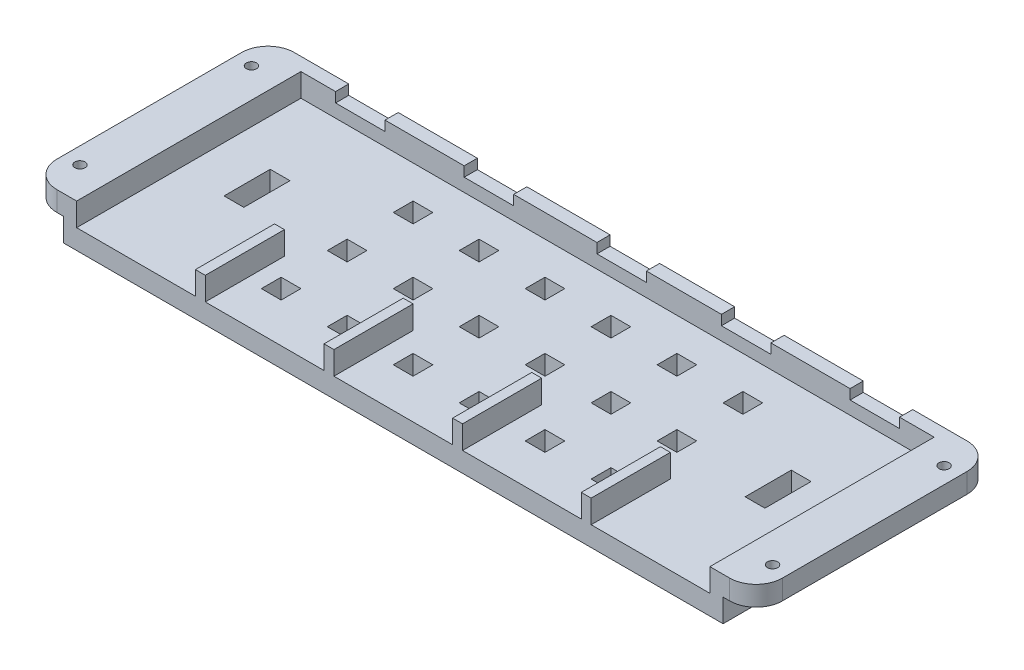
SolidWorks part; units mm, degrees
ref_plane "Спереди" through (0, 0, 0) normal (0, 0, 1) x (1, 0, 0)
ref_plane "Сверху" through (0, 0, 0) normal (0, 1, 0) x (1, 0, 0)
ref_plane "Справа" through (0, 0, 0) normal (1, 0, 0) x (0, 0, -1)
sketch "Sketch1" plane through (0, 0, 0) normal (0, 1, 0) x (1, 0, 0)
  line L1 (-36.9177, 8.4416) -> (63.0823, 8.4416)
  line L2 (-36.9177, 8.4416) -> (-36.9177, -27.5584)
  line L3 (-36.9177, -27.5584) -> (63.0823, -27.5584)
  line L4 (63.0823, 8.4416) -> (63.0823, -27.5584)
  dimension "D1" = 100
  dimension "D2" = 36
extrude "Boss-Extrude1" add sketch "Sketch1" along normal blind 3
sketch "Sketch2" plane through (0, 3, 0) normal (0, 1, 0) x (1, 0, 0)
  line L1 (-36.9177, 8.4416) -> (63.0823, 8.4416)
  line L2 (-36.9177, 8.4416) -> (-36.9177, -27.5584)
  line L3 (-36.9177, -27.5584) -> (63.0823, -27.5584)
  line L4 (63.0823, 8.4416) -> (63.0823, -27.5584)
  line L5 (-34.9177, 6.4416) -> (61.0823, 6.4416)
  line L6 (-34.9177, 6.4416) -> (-34.9177, -25.5584)
  line L7 (-34.9177, -25.5584) -> (61.0823, -25.5584)
  line L8 (61.0823, 6.4416) -> (61.0823, -25.5584)
  dimension "D1" = 2
  dimension "D2" = 2
  dimension "D3" = 2
  dimension "D4" = 2
extrude "Boss-Extrude2" add sketch "Sketch2" along normal blind 3.5
sketch "Sketch4" plane through (0, 6.5, 0) normal (0, 1, 0) x (1, 0, 0)
  line L0 (-34.9177, -25.5584) -> (61.0823, -25.5584) construction
  line L1 (-34.9177, -25.5584) -> (-16.9177, -25.5584)
  line L2 (-34.9177, -25.5584) -> (-34.9177, -27.5584)
  line L3 (-34.9177, -27.5584) -> (-16.9177, -27.5584)
  line L4 (-16.9177, -25.5584) -> (-16.9177, -27.5584)
  line L5 (-36.9177, -27.5584) -> (63.0823, -27.5584) construction
  line L6 (-34.9177, -25.5584) -> (61.0823, -25.5584) construction
  line L7 (-15.4177, -25.5584) -> (2.5823, -25.5584)
  line L8 (-15.4177, -25.5584) -> (-15.4177, -27.5584)
  line L9 (-15.4177, -27.5584) -> (2.5823, -27.5584)
  line L10 (2.5823, -25.5584) -> (2.5823, -27.5584)
  line L11 (-34.9177, 6.4416) -> (-34.9177, -25.5584) construction
  line L12 (4.0823, -25.5584) -> (22.0823, -25.5584)
  line L13 (4.0823, -25.5584) -> (4.0823, -27.5584)
  line L14 (4.0823, -27.5584) -> (22.0823, -27.5584)
  line L15 (22.0823, -25.5584) -> (22.0823, -27.5584)
  line L16 (23.5823, -25.5584) -> (41.5823, -25.5584)
  line L17 (23.5823, -25.5584) -> (23.5823, -27.5584)
  line L18 (23.5823, -27.5584) -> (41.5823, -27.5584)
  line L19 (41.5823, -25.5584) -> (41.5823, -27.5584)
  line L20 (43.0823, -25.5584) -> (61.0823, -25.5584)
  line L21 (43.0823, -25.5584) -> (43.0823, -27.5584)
  line L22 (43.0823, -27.5584) -> (61.0823, -27.5584)
  line L23 (61.0823, -25.5584) -> (61.0823, -27.5584)
  line L24 (-25.9177, -27.5584) -> (-25.9177, 8.4416) construction
  line L25 (63.0823, 8.4416) -> (-36.9177, 8.4416) construction
  line L26 (-6.4177, -27.5584) -> (-6.4177, 8.4416) construction
  line L27 (13.0823, -27.5584) -> (13.7084, 8.4416) construction
  line L28 (32.5823, -27.5584) -> (32.5823, 8.4416) construction
  line L29 (52.0823, -27.5584) -> (52.0823, 8.4416) construction
  line L30 (61.0823, 6.4416) -> (-34.9177, 6.4416) construction
  line L31 (-29.6677, 8.4416) -> (-22.1677, 8.4416)
  line L32 (-29.6677, 8.4416) -> (-29.6677, 6.4416)
  line L33 (-29.6677, 6.4416) -> (-22.1677, 6.4416)
  line L34 (-22.1677, 8.4416) -> (-22.1677, 6.4416)
  line L36 (-10.1677, 8.4416) -> (-2.6677, 8.4416)
  line L37 (-10.1677, 8.4416) -> (-10.1677, 6.4416)
  line L38 (-10.1677, 6.4416) -> (-2.6677, 6.4416)
  line L39 (-2.6677, 8.4416) -> (-2.6677, 6.4416)
  line L40 (9.9584, 8.4416) -> (17.4584, 8.4416)
  line L41 (9.9584, 8.4416) -> (9.9584, 6.4416)
  line L42 (9.9584, 6.4416) -> (17.4584, 6.4416)
  line L43 (17.4584, 8.4416) -> (17.4584, 6.4416)
  line L44 (28.8323, 8.4416) -> (36.3323, 8.4416)
  line L45 (28.8323, 8.4416) -> (28.8323, 6.4416)
  line L46 (28.8323, 6.4416) -> (36.3323, 6.4416)
  line L47 (36.3323, 8.4416) -> (36.3323, 6.4416)
  line L48 (48.3323, 8.4416) -> (55.8323, 8.4416)
  line L49 (48.3323, 8.4416) -> (48.3323, 6.4416)
  line L50 (48.3323, 6.4416) -> (55.8323, 6.4416)
  line L51 (55.8323, 8.4416) -> (55.8323, 6.4416)
  point P62 (0, 0)
  point P63 (0, 0)
  point P64 (0, 0)
  point P65 (0, 0)
  point P66 (0, 0)
  point P67 (0, 0)
  dimension "D1" = 18
  dimension "D2" = 1.5
  dimension "D3" = 1.5
  dimension "D4" = 1.5
  dimension "D5" = 1.5
  dimension "D6" = 7.5
extrude "Cut-Extrude1" cut sketch "Sketch4" against normal blind 3.5
sketch "Sketch5" plane through (0, 0, 25.5584) normal (0, 0, -1) x (-1, 0, 0)
  line L1 (15.4177, 6.5) -> (16.9177, 6.5)
  line L2 (15.4177, 6.5) -> (15.4177, 3)
  line L3 (15.4177, 3) -> (16.9177, 3)
  line L4 (16.9177, 6.5) -> (16.9177, 3)
  line L5 (-4.0823, 6.5) -> (-2.5823, 6.5)
  line L6 (-4.0823, 6.5) -> (-4.0823, 3)
  line L7 (-4.0823, 3) -> (-2.5823, 3)
  line L8 (-2.5823, 6.5) -> (-2.5823, 3)
  line L9 (-23.5823, 6.5) -> (-22.0823, 6.5)
  line L10 (-23.5823, 6.5) -> (-23.5823, 3)
  line L11 (-23.5823, 3) -> (-22.0823, 3)
  line L12 (-22.0823, 6.5) -> (-22.0823, 3)
  line L13 (-43.0823, 6.5) -> (-41.5823, 6.5)
  line L14 (-43.0823, 6.5) -> (-43.0823, 3)
  line L15 (-43.0823, 3) -> (-41.5823, 3)
  line L16 (-41.5823, 6.5) -> (-41.5823, 3)
extrude "Boss-Extrude3" add sketch "Sketch5" along normal blind 10
sketch "Sketch6" plane through (0, 3, 0) normal (0, 1, 0) x (1, 0, 0)
  line L1 (-29.6677, 8.4416) -> (-22.1677, 8.4416)
  line L2 (-29.6677, 8.4416) -> (-29.6677, 6.4416)
  line L3 (-29.6677, 6.4416) -> (-22.1677, 6.4416)
  line L4 (-22.1677, 8.4416) -> (-22.1677, 6.4416)
  line L5 (-10.1677, 8.4416) -> (-2.6677, 8.4416)
  line L6 (-10.1677, 8.4416) -> (-10.1677, 6.4416)
  line L7 (-10.1677, 6.4416) -> (-2.6677, 6.4416)
  line L8 (-2.6677, 8.4416) -> (-2.6677, 6.4416)
  line L9 (9.9584, 8.4416) -> (17.4584, 8.4416)
  line L10 (9.9584, 8.4416) -> (9.9584, 6.4416)
  line L11 (9.9584, 6.4416) -> (17.4584, 6.4416)
  line L12 (17.4584, 8.4416) -> (17.4584, 6.4416)
  line L13 (28.8323, 8.4416) -> (36.3323, 8.4416)
  line L14 (28.8323, 8.4416) -> (28.8323, 6.4416)
  line L15 (28.8323, 6.4416) -> (36.3323, 6.4416)
  line L16 (36.3323, 8.4416) -> (36.3323, 6.4416)
  line L17 (48.3323, 8.4416) -> (55.8323, 8.4416)
  line L18 (48.3323, 8.4416) -> (48.3323, 6.4416)
  line L19 (48.3323, 6.4416) -> (55.8323, 6.4416)
  line L20 (55.8323, 8.4416) -> (55.8323, 6.4416)
extrude "Boss-Extrude4" add sketch "Sketch6" along normal blind 2
sketch "Sketch7" plane through (-36.9177, 0, 0) normal (-1, 0, 0) x (0, 0, 1)
  line L0 (27.5584, 6.5) -> (27.5584, 0) construction
  line L1 (-8.4416, 6.5) -> (27.5584, 6.5)
  line L2 (-8.4416, 6.5) -> (-8.4416, 3.5)
  line L3 (-8.4416, 3.5) -> (27.5584, 3.5)
  line L4 (27.5584, 6.5) -> (27.5584, 3.5)
  dimension "D1" = 3
extrude "Boss-Extrude5" add sketch "Sketch7" along normal blind 5
sketch "Sketch8" plane through (63.0823, 0, 0) normal (1, 0, 0) x (0, 0, -1)
  line L0 (-27.5584, 6.5) -> (-27.5584, 0) construction
  line L1 (8.4416, 6.5) -> (-27.5584, 6.5)
  line L2 (8.4416, 6.5) -> (8.4416, 3.5)
  line L3 (8.4416, 3.5) -> (-27.5584, 3.5)
  line L4 (-27.5584, 6.5) -> (-27.5584, 3.5)
  dimension "D1" = 3
extrude "Boss-Extrude6" add sketch "Sketch8" along normal blind 5
sketch "Sketch9" plane through (0, 3.5, 0) normal (0, -1, 0) x (1, 0, 0)
  line L0 (-41.9177, 27.5584) -> (-36.9177, 27.5584) construction
  line L1 (-41.9177, -8.4416) -> (-41.9177, 27.5584) construction
  line L2 (-41.9177, -8.4416) -> (-36.9177, -8.4416) construction
  line L3 (68.0823, 27.5584) -> (68.0823, -8.4416) construction
  line L4 (68.0823, 27.5584) -> (63.0823, 27.5584) construction
  line L5 (68.0823, -8.4416) -> (63.0823, -8.4416) construction
  circle A0 centre (-39.4177, 22.5584) radius 0.775
  circle A1 centre (-39.4177, -3.4416) radius 0.775
  circle A2 centre (65.5823, 22.5584) radius 0.775
  circle A3 centre (65.5823, -3.4416) radius 0.775
  point P18 (49.743, 25.9963)
  dimension "D9" = 1.55
  dimension "D1" = 5
  dimension "D2" = 2.5
  dimension "D3" = 2.5
  dimension "D4" = 5
  dimension "D5" = 2.5
  dimension "D6" = 5
  dimension "D7" = 5
  dimension "D8" = 2.5
extrude "Cut-Extrude2" cut sketch "Sketch9" against normal through all
sketch "Sketch10" plane through (0, 3.5, 0) normal (0, -1, 0) x (1, 0, 0)
  circle A0 centre (-39.4177, 22.5584) radius 1.275
  circle A1 centre (-39.4177, -3.4416) radius 1.275
  circle A2 centre (65.5823, 22.5584) radius 1.275
  circle A3 centre (65.5823, -3.4416) radius 1.275
  dimension "D1" = 2.55
extrude "Cut-Extrude3" cut sketch "Sketch10" against normal blind 1
fillet "Fillet1" radius 4 4 edges at (-41.9177, 5, 27.5584) (-41.9177, 5, -8.4416) (68.0823, 5, -8.4416) (68.0823, 5, 27.5584)
sketch "Sketch11" plane through (0, 0, 0) normal (0, -1, 0) x (1, 0, 0)
  line L0 (-31.9177, 20.0584) -> (-21.9177, 20.0584) construction
  line L1 (-31.9177, 22.5584) -> (-21.9177, 22.5584)
  line L2 (-31.9177, 17.5584) -> (-21.9177, 17.5584)
  line L3 (-36.9177, 27.5584) -> (63.0823, 27.5584) construction
  line L4 (-36.9177, -8.4416) -> (-36.9177, 27.5584) construction
  line L5 (48.0823, 20.0584) -> (58.0823, 20.0584) construction
  line L6 (48.0823, 22.5584) -> (58.0823, 22.5584)
  line L7 (48.0823, 17.5584) -> (58.0823, 17.5584)
  line L8 (48.0823, -0.9416) -> (58.0823, -0.9416) construction
  line L9 (48.0823, 1.5584) -> (58.0823, 1.5584)
  line L10 (48.0823, -3.4416) -> (58.0823, -3.4416)
  line L11 (-31.9177, -0.9416) -> (-21.9177, -0.9416) construction
  line L12 (-31.9177, 1.5584) -> (-21.9177, 1.5584)
  line L13 (-31.9177, -3.4416) -> (-21.9177, -3.4416)
  arc A0 (-31.9177, 22.5584) -> (-31.9177, 17.5584) centre (-31.9177, 20.0584) ccw
  arc A1 (-21.9177, 17.5584) -> (-21.9177, 22.5584) centre (-21.9177, 20.0584) ccw
  arc A2 (48.0823, 22.5584) -> (48.0823, 17.5584) centre (48.0823, 20.0584) ccw
  arc A3 (58.0823, 17.5584) -> (58.0823, 22.5584) centre (58.0823, 20.0584) ccw
  arc A4 (48.0823, 1.5584) -> (48.0823, -3.4416) centre (48.0823, -0.9416) ccw
  arc A5 (58.0823, -3.4416) -> (58.0823, 1.5584) centre (58.0823, -0.9416) ccw
  arc A6 (-31.9177, 1.5584) -> (-31.9177, -3.4416) centre (-31.9177, -0.9416) ccw
  arc A7 (-21.9177, -3.4416) -> (-21.9177, 1.5584) centre (-21.9177, -0.9416) ccw
  point P2 (-26.9177, 20.0584)
  point P16 (53.0823, 20.0584)
  point P23 (53.0823, -0.9416)
  point P30 (-26.9177, -0.9416)
  dimension "D1" = 10
  dimension "D2" = 5
  dimension "D3" = 5
  dimension "D4" = 5
  dimension "D5" = 2
  dimension "D6" = 2
extrude "Boss-Extrude7" add sketch "Sketch11" along normal blind 3
fillet "Fillet2" radius 2 16 edges at (-34.4177, -3, -0.9416) (-26.9177, -3, -3.4416) (-19.4177, -3, -0.9416) (-26.9177, -3, 1.5584) (45.5823, -3, -0.9416) (53.0823, -3, -3.4416) (60.5823, -3, -0.9416) (53.0823, -3, 1.5584) (45.5823, -3, 20.0584) (53.0823, -3, 17.5584) (60.5823, -3, 20.0584) (53.0823, -3, 22.5584) (-34.4177, -3, 20.0584) (-26.9177, -3, 17.5584) (-19.4177, -3, 20.0584) (-26.9177, -3, 22.5584)
sketch "Sketch12" plane through (0, 0, 0) normal (0, -1, 0) x (1, 0, 0)
  line L0 (-36.9177, -8.4416) -> (-36.9177, 27.5584) construction
  line L1 (-12.9177, 21.5584) -> (-9.9177, 21.5584)
  line L2 (-12.9177, 21.5584) -> (-12.9177, 18.5584)
  line L3 (-12.9177, 18.5584) -> (-9.9177, 18.5584)
  line L4 (-9.9177, 21.5584) -> (-9.9177, 18.5584)
  line L5 (-36.9177, 27.5584) -> (63.0823, 27.5584) construction
  line L6 (-2.9177, 21.5584) -> (0.0823, 21.5584)
  line L7 (0.0823, 21.5584) -> (0.0823, 18.5584)
  line L8 (-2.9177, 18.5584) -> (0.0823, 18.5584)
  line L9 (-2.9177, 21.5584) -> (-2.9177, 18.5584)
  line L10 (7.0823, 21.5584) -> (10.0823, 21.5584)
  line L11 (10.0823, 21.5584) -> (10.0823, 18.5584)
  line L12 (7.0823, 18.5584) -> (10.0823, 18.5584)
  line L13 (7.0823, 21.5584) -> (7.0823, 18.5584)
  line L14 (17.0823, 21.5584) -> (20.0823, 21.5584)
  line L15 (20.0823, 21.5584) -> (20.0823, 18.5584)
  line L16 (17.0823, 18.5584) -> (20.0823, 18.5584)
  line L17 (17.0823, 21.5584) -> (17.0823, 18.5584)
  line L18 (27.0823, 21.5584) -> (30.0823, 21.5584)
  line L19 (30.0823, 21.5584) -> (30.0823, 18.5584)
  line L20 (27.0823, 18.5584) -> (30.0823, 18.5584)
  line L21 (27.0823, 21.5584) -> (27.0823, 18.5584)
  line L22 (37.0823, 21.5584) -> (40.0823, 21.5584)
  line L23 (40.0823, 21.5584) -> (40.0823, 18.5584)
  line L24 (37.0823, 18.5584) -> (40.0823, 18.5584)
  line L25 (37.0823, 21.5584) -> (37.0823, 18.5584)
  line L26 (-2.9177, 11.5584) -> (0.0823, 11.5584)
  line L27 (0.0823, 11.5584) -> (0.0823, 8.5584)
  line L28 (-2.9177, 8.5584) -> (0.0823, 8.5584)
  line L29 (-2.9177, 11.5584) -> (-2.9177, 8.5584)
  line L30 (7.0823, 11.5584) -> (10.0823, 11.5584)
  line L31 (10.0823, 11.5584) -> (10.0823, 8.5584)
  line L32 (7.0823, 8.5584) -> (10.0823, 8.5584)
  line L33 (7.0823, 11.5584) -> (7.0823, 8.5584)
  line L34 (17.0823, 11.5584) -> (20.0823, 11.5584)
  line L35 (20.0823, 11.5584) -> (20.0823, 8.5584)
  line L36 (17.0823, 8.5584) -> (20.0823, 8.5584)
  line L37 (17.0823, 11.5584) -> (17.0823, 8.5584)
  line L38 (27.0823, 11.5584) -> (30.0823, 11.5584)
  line L39 (30.0823, 11.5584) -> (30.0823, 8.5584)
  line L40 (27.0823, 8.5584) -> (30.0823, 8.5584)
  line L41 (27.0823, 11.5584) -> (27.0823, 8.5584)
  line L42 (37.0823, 11.5584) -> (40.0823, 11.5584)
  line L43 (40.0823, 11.5584) -> (40.0823, 8.5584)
  line L44 (37.0823, 8.5584) -> (40.0823, 8.5584)
  line L45 (37.0823, 11.5584) -> (37.0823, 8.5584)
  line L46 (-2.9177, 1.5584) -> (0.0823, 1.5584)
  line L47 (0.0823, 1.5584) -> (0.0823, -1.4416)
  line L48 (-2.9177, -1.4416) -> (0.0823, -1.4416)
  line L49 (-2.9177, 1.5584) -> (-2.9177, -1.4416)
  line L50 (7.0823, 1.5584) -> (10.0823, 1.5584)
  line L51 (10.0823, 1.5584) -> (10.0823, -1.4416)
  line L52 (7.0823, -1.4416) -> (10.0823, -1.4416)
  line L53 (7.0823, 1.5584) -> (7.0823, -1.4416)
  line L54 (17.0823, 1.5584) -> (20.0823, 1.5584)
  line L55 (20.0823, 1.5584) -> (20.0823, -1.4416)
  line L56 (17.0823, -1.4416) -> (20.0823, -1.4416)
  line L57 (17.0823, 1.5584) -> (17.0823, -1.4416)
  line L58 (27.0823, 1.5584) -> (30.0823, 1.5584)
  line L59 (30.0823, 1.5584) -> (30.0823, -1.4416)
  line L60 (27.0823, -1.4416) -> (30.0823, -1.4416)
  line L61 (27.0823, 1.5584) -> (27.0823, -1.4416)
  line L62 (37.0823, 1.5584) -> (40.0823, 1.5584)
  line L63 (40.0823, 1.5584) -> (40.0823, -1.4416)
  line L64 (37.0823, -1.4416) -> (40.0823, -1.4416)
  line L65 (37.0823, 1.5584) -> (37.0823, -1.4416)
  line L66 (-12.9177, 11.5584) -> (-9.9177, 11.5584)
  line L67 (-9.9177, 11.5584) -> (-9.9177, 8.5584)
  line L68 (-12.9177, 8.5584) -> (-9.9177, 8.5584)
  line L69 (-12.9177, 11.5584) -> (-12.9177, 8.5584)
  line L70 (-12.9177, 1.5584) -> (-9.9177, 1.5584)
  line L71 (-9.9177, 1.5584) -> (-9.9177, -1.4416)
  line L72 (-12.9177, -1.4416) -> (-9.9177, -1.4416)
  line L73 (-12.9177, 1.5584) -> (-12.9177, -1.4416)
  line L74 (-36.9177, -8.4416) -> (-36.9177, 27.5584) construction
  line L75 (-27.9177, 12.2151) -> (-24.9177, 12.2151)
  line L76 (-27.9177, 12.2151) -> (-27.9177, 5.2151)
  line L77 (-27.9177, 5.2151) -> (-24.9177, 5.2151)
  line L78 (-24.9177, 12.2151) -> (-24.9177, 5.2151)
  line L79 (51.0823, 12.2151) -> (54.0823, 12.2151)
  line L80 (51.0823, 12.2151) -> (51.0823, 5.2151)
  line L81 (51.0823, 5.2151) -> (54.0823, 5.2151)
  line L82 (54.0823, 12.2151) -> (54.0823, 5.2151)
  line L83 (63.0823, 27.5584) -> (63.0823, -8.4416) construction
  point P84 (-31.5093, 11.5853)
  dimension "D1" = 3
  dimension "D2" = 3
  dimension "D3" = 24
  dimension "D4" = 6
  dimension "D7" = 7
  dimension "D8" = 3
  dimension "D9" = 9
  dimension "D10" = 9
  dimension "D5" = 6
  dimension "D6" = 3
extrude "Cut-Extrude4" cut sketch "Sketch12" against normal through all
